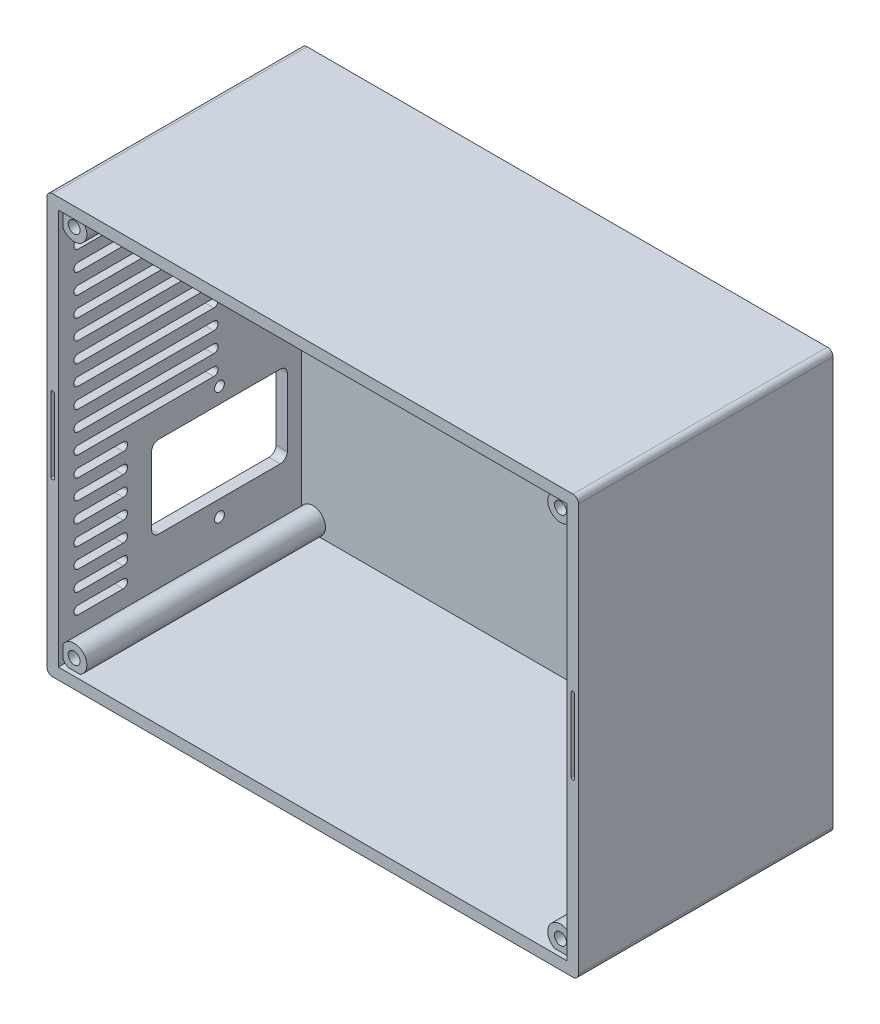
SolidWorks part; units mm, degrees
ref_plane "Alzado" through (0, 0, 0) normal (0, 0, 1) x (1, 0, 0)
ref_plane "Planta" through (0, 0, 0) normal (0, 1, 0) x (1, 0, 0)
ref_plane "Vista lateral" through (0, 0, 0) normal (1, 0, 0) x (0, 0, -1)
sketch "Croquis1" plane through (0, 0, 0) normal (0, 0, 1) x (1, 0, 0)
  line L0 (0, 0) -> (0, 140) construction
  line L5 (0, 140) -> (180, 140) construction
  line L6 (180, 140) -> (180, 0) construction
  line L7 (180, 0) -> (0, 0) construction
  line L9 (-4, 144) -> (184, 144)
  line L10 (-4, 144) -> (-4, -4)
  line L11 (-4, -4) -> (184, -4)
  line L12 (184, 144) -> (184, -4)
  dimension "D1" = 140
  dimension "D2" = 180
  dimension "D3" = 4
  dimension "D4" = 4
  dimension "D5" = 4
  dimension "D6" = 4
extrude "Saliente-Extruir1" add sketch "Croquis1" along normal blind 90 contours L9 L12 L11 L10
ref_plane "Plano2" through (0, 0, 4) normal (0, 0, -1) x (-1, 0, 0)
sketch "Croquis6" plane through (0, 0, 4) normal (0, 0, -1) x (-1, 0, 0)
  line L1 (0, 140) -> (-180, 140)
  line L2 (0, 140) -> (0, 0)
  line L3 (0, 0) -> (-180, 0)
  line L4 (-180, 140) -> (-180, 0)
  line L5 (4, 144) -> (-184, 144) construction
  line L6 (4, 144) -> (4, -4) construction
  line L7 (4, -4) -> (-184, -4) construction
  line L8 (-184, 144) -> (-184, -4) construction
  dimension "D3" = 4
  dimension "D1" = 4
  dimension "D2" = 4
  dimension "D4" = 4
extrude "Cortar-Extruir1" cut sketch "Croquis6" against normal through all
sketch "Croquis7" plane through (0, 0, 4) normal (0, 0, -1) x (-1, 0, 0)
  line L0 (0, 140) -> (-180, 140) construction
  line L1 (-4, 136) -> (-176, 136)
  line L2 (-4, 136) -> (-4, 4)
  line L3 (-4, 4) -> (-176, 4)
  line L4 (-176, 136) -> (-176, 4)
  line L5 (0, 0) -> (0, 140) construction
  line L6 (-180, 0) -> (0, 0) construction
  line L7 (-180, 140) -> (-180, 0) construction
  circle A0 centre (-4, 136) radius 4.4996
  circle A5 centre (-176, 136) radius 4.4996
  circle A6 centre (-176, 4) radius 4.4996
  circle A8 centre (-4, 4) radius 4.4996
  dimension "D3" = 4
  dimension "D1" = 4
  dimension "D4" = 4
  dimension "D7" = 8.9993
  dimension "D5" = 8.9993
  dimension "D6" = 8.9993
  dimension "D8" = 8.9993
  dimension "D2" = 4
extrude "Saliente-Extruir2" add sketch "Croquis7" against normal blind 84.4
sketch "Croquis9" plane through (0, 0, 4) normal (0, 0, -1) x (-1, 0, 0)
  line L1 (-4, 136) -> (-176, 136)
  line L2 (-4, 136) -> (-4, 4)
  line L3 (-4, 4) -> (-176, 4)
  line L4 (-176, 136) -> (-176, 4)
  circle A0 centre (-4, 136) radius 2.1
  circle A1 centre (-176, 136) radius 2.1
  circle A2 centre (-176, 4) radius 2.1
  circle A3 centre (-4, 4) radius 2.1
  dimension "D1" = 4.2
  dimension "D4" = 4.2
  dimension "D5" = 4.2
  dimension "D6" = 4.2
  dimension "D2" = 132
  dimension "D3" = 172
extrude "Cortar-Extruir3" cut sketch "Croquis9" against normal up to next contours A0 | A1 | A2 | A3
fillet "Redondeo1" radius 2 4 edges at (184, 144, 45) (184, -4, 45) (-4, -4, 45) (-4, 144, 45)
sketch "Croquis10" plane through (0, 0, 4) normal (0, 0, -1) x (-1, 0, 0)
  line L0 (2, 144) -> (-182, 144) construction
  line L1 (-16, 124) -> (-164, 124)
  line L2 (-16, 124) -> (-16, 16)
  line L3 (-16, 16) -> (-164, 16)
  line L4 (-164, 124) -> (-164, 16)
  line L5 (4, 142) -> (4, -2) construction
  line L6 (2, -4) -> (-182, -4) construction
  line L7 (-184, 142) -> (-184, -2) construction
  circle A0 centre (-16, 124) radius 7.5
  circle A1 centre (-164, 124) radius 7.5
  circle A2 centre (-164, 16) radius 7.5
  circle A3 centre (-16, 16) radius 7.5
  dimension "D5" = 15
  dimension "D6" = 15
  dimension "D7" = 15
  dimension "D8" = 15
  dimension "D1" = 20
  dimension "D2" = 20
  dimension "D3" = 20
  dimension "D4" = 20
extrude "Cortar-Extruir4" cut sketch "Croquis10" along normal through all from offset 2 contours A0 | A1 | A2 | A3
ref_plane "Plano3" through (-4, 0, 0) normal (-1, 0, 0) x (0, 0, 1)
sketch "Croquis11" plane through (-4, 0, 0) normal (-1, 0, 0) x (0, 0, 1)
  line L0 (9, 37.5) -> (57, 37.5) construction
  line L1 (11.5, 52) -> (54.5, 52)
  line L2 (9, 49.5) -> (9, 25.5)
  line L3 (11.5, 23) -> (54.5, 23)
  line L4 (57, 49.5) -> (57, 25.5)
  line L5 (33, 52) -> (33, 23) construction
  line L6 (0, 142) -> (0, -2) construction
  line L7 (0, -2) -> (90, -2) construction
  arc A0 (9, 25.5) -> (11.5, 23) centre (11.5, 25.5) ccw
  arc A1 (54.5, 23) -> (57, 25.5) centre (54.5, 25.5) ccw
  arc A2 (54.5, 52) -> (57, 49.5) centre (54.5, 49.5) cw
  arc A3 (11.5, 52) -> (9, 49.5) centre (11.5, 49.5) ccw
  circle A4 centre (33, 57.5) radius 1.75
  circle A5 centre (33, 17.5) radius 1.75
  point P8 (57, 23)
  point P11 (57, 52)
  point P14 (9, 52)
  point P27 (33, 48.1213)
  point P28 (33, 6.626)
  point P29 (0, 0)
  point P30 (0, 0)
  point P31 (0, 0)
  point P32 (0, 0)
  point P33 (0, 0)
  point P34 (0, 0)
  point P35 (33, 16.1617)
  point P36 (33, 40.8738)
  dimension "D3" = 2.5
  dimension "D4" = 9
  dimension "D5" = 25
  dimension "D6" = 20
  dimension "D8" = 3.5
  dimension "D9" = 3.5
  dimension "D1" = 48
  dimension "D2" = 29
  dimension "D7" = 20
sketch "Croquis12" plane through (0, 0, 4) normal (0, 0, -1) x (-1, 0, 0)
  line L0 (0, 140) -> (-180, 140) construction
  line L1 (-180, 133.9392) -> (-180, 6.0608) construction
  circle A1 centre (-93, 125) radius 2.1
  circle A2 centre (-93, 54) radius 2.1
  point P2 (0, 0)
  point P3 (0, 0)
  point P8 (0, 0)
  dimension "D3" = 15
  dimension "D4" = 4.2
  dimension "D1" = 4.2
  dimension "D2" = 71
  dimension "D5" = 87
ref_plane "Plano4" through (0, 140, 0) normal (0, -1, 0) x (-1, 0, 0)
sketch "Croquis15" plane through (0, 0, 4) normal (0, 0, -1) x (-1, 0, 0)
  line L0 (2, 144) -> (-182, 144) construction
  line L1 (-164, 114) -> (-124, 114)
  line L2 (-164, 114) -> (-164, 74)
  line L3 (-164, 74) -> (-124, 74)
  line L4 (-124, 114) -> (-124, 74)
  line L5 (-184, 142) -> (-184, -2) construction
  line L7 (-160.5, 110.5) -> (-127.5, 110.5)
  line L8 (-160.5, 110.5) -> (-160.5, 77.5)
  line L9 (-160.5, 77.5) -> (-127.5, 77.5)
  line L10 (-127.5, 110.5) -> (-127.5, 77.5)
  circle A0 centre (-160.5, 110.5) radius 1.75
  circle A1 centre (-127.5, 110.5) radius 1.75
  circle A2 centre (-127.5, 77.5) radius 1.75
  circle A3 centre (-160.5, 77.5) radius 1.75
  dimension "D4" = 20
  dimension "D9" = 3.5
  dimension "D10" = 3.5
  dimension "D11" = 3.5
  dimension "D12" = 3.5
  dimension "D1" = 40
  dimension "D2" = 40
  dimension "D3" = 30
  dimension "D5" = 33
  dimension "D6" = 33
  dimension "D7" = 3.5
  dimension "D8" = 3.5
extrude "Cortar-Extruir19" cut sketch "Croquis15" along normal up to next (4 mm away) contours A0 | A1 | A3 | A2
sketch "Croquis17" plane through (0, 0, 4) normal (0, 0, -1) x (-1, 0, 0)
  line L0 (-164, 94) -> (-124, 94) construction
  line L1 (-164, 114) -> (-164, 74) construction
  line L2 (-124, 114) -> (-124, 74) construction
  line L3 (-144, 114) -> (-144, 74) construction
  line L4 (-164, 114) -> (-124, 114) construction
  line L5 (-164, 74) -> (-124, 74) construction
  line L6 (-144, 113.1) -> (-144, 103.1) construction
  line L11 (-143.25, 113.1) -> (-143.25, 103.1)
  line L12 (-144.75, 113.1) -> (-144.75, 103.1)
  line L13 (-140.1573, 112.7245) -> (-142.5504, 103.0151)
  line L14 (-138.7009, 112.3655) -> (-141.094, 102.6561)
  line L15 (-139.4291, 112.545) -> (-141.8222, 102.8356) construction
  line L16 (-135.7879, 111.2608) -> (-140.4351, 102.4062)
  line L17 (-134.4597, 110.5637) -> (-139.1069, 101.7091)
  line L18 (-135.1238, 110.9122) -> (-139.771, 102.0576) construction
  line L19 (-131.8957, 108.7939) -> (-138.527, 101.3088)
  line L20 (-130.773, 107.7992) -> (-137.4042, 100.3141)
  line L21 (-131.3344, 108.2966) -> (-137.9656, 100.8114) construction
  line L22 (-128.7071, 105.4673) -> (-136.9369, 99.7866)
  line L23 (-127.855, 104.2328) -> (-136.0848, 98.5522)
  line L24 (-128.281, 104.85) -> (-136.5108, 99.1694) construction
  line L25 (-126.4071, 101.4742) -> (-135.7573, 97.9282)
  line L26 (-125.8752, 100.0717) -> (-135.2254, 96.5256)
  line L27 (-126.1412, 100.773) -> (-135.4914, 97.2269) construction
  line L28 (-125.1297, 97.0468) -> (-135.0568, 95.8414)
  line L29 (-124.9489, 95.5577) -> (-134.8759, 94.3524)
  line L30 (-125.0393, 96.3023) -> (-134.9663, 95.0969) construction
  line L31 (-124.9489, 92.4423) -> (-134.8759, 93.6476)
  line L32 (-125.1297, 90.9532) -> (-135.0568, 92.1586)
  line L33 (-125.0393, 91.6977) -> (-134.9663, 92.9031) construction
  line L34 (-125.8752, 87.9283) -> (-135.2254, 91.4744)
  line L35 (-126.4071, 86.5258) -> (-135.7573, 90.0718)
  line L36 (-126.1412, 87.227) -> (-135.4914, 90.7731) construction
  line L37 (-127.855, 83.7672) -> (-136.0848, 89.4478)
  line L38 (-128.7071, 82.5327) -> (-136.9369, 88.2134)
  line L39 (-128.281, 83.15) -> (-136.5108, 88.8306) construction
  line L40 (-130.773, 80.2008) -> (-137.4042, 87.6859)
  line L41 (-131.8957, 79.2061) -> (-138.527, 86.6912)
  line L42 (-131.3344, 79.7034) -> (-137.9656, 87.1886) construction
  line L43 (-134.4597, 77.4363) -> (-139.1069, 86.2909)
  line L44 (-135.7879, 76.7392) -> (-140.4351, 85.5938)
  line L45 (-135.1238, 77.0878) -> (-139.771, 85.9424) construction
  line L46 (-138.7009, 75.6345) -> (-141.094, 85.3439)
  line L47 (-140.1573, 75.2755) -> (-142.5504, 84.9849)
  line L48 (-139.4291, 75.455) -> (-141.8222, 85.1644) construction
  line L49 (-143.25, 74.9) -> (-143.25, 84.9)
  line L50 (-144.75, 74.9) -> (-144.75, 84.9)
  line L51 (-144, 74.9) -> (-144, 84.9) construction
  line L52 (-147.8427, 75.2755) -> (-145.4496, 84.9849)
  line L53 (-149.2991, 75.6345) -> (-146.906, 85.3439)
  line L54 (-148.5709, 75.455) -> (-146.1778, 85.1644) construction
  line L55 (-152.2121, 76.7392) -> (-147.5649, 85.5938)
  line L56 (-153.5403, 77.4363) -> (-148.8931, 86.2909)
  line L57 (-152.8762, 77.0878) -> (-148.229, 85.9424) construction
  line L58 (-156.1043, 79.2061) -> (-149.473, 86.6912)
  line L59 (-157.227, 80.2008) -> (-150.5958, 87.6859)
  line L60 (-156.6656, 79.7034) -> (-150.0344, 87.1886) construction
  line L61 (-159.2929, 82.5327) -> (-151.0631, 88.2134)
  line L62 (-160.145, 83.7672) -> (-151.9152, 89.4478)
  line L63 (-159.719, 83.15) -> (-151.4892, 88.8306) construction
  line L64 (-161.5929, 86.5258) -> (-152.2427, 90.0718)
  line L65 (-162.1248, 87.9283) -> (-152.7746, 91.4744)
  line L66 (-161.8588, 87.227) -> (-152.5086, 90.7731) construction
  line L67 (-162.8703, 90.9532) -> (-152.9432, 92.1586)
  line L68 (-163.0511, 92.4423) -> (-153.1241, 93.6476)
  line L69 (-162.9607, 91.6977) -> (-153.0337, 92.9031) construction
  line L70 (-163.0511, 95.5577) -> (-153.1241, 94.3524)
  line L71 (-162.8703, 97.0468) -> (-152.9432, 95.8414)
  line L72 (-162.9607, 96.3023) -> (-153.0337, 95.0969) construction
  line L73 (-162.1248, 100.0717) -> (-152.7746, 96.5256)
  line L74 (-161.5929, 101.4742) -> (-152.2427, 97.9282)
  line L75 (-161.8588, 100.773) -> (-152.5086, 97.2269) construction
  line L76 (-160.145, 104.2328) -> (-151.9152, 98.5522)
  line L77 (-159.2929, 105.4673) -> (-151.0631, 99.7866)
  line L78 (-159.719, 104.85) -> (-151.4892, 99.1694) construction
  line L79 (-157.227, 107.7992) -> (-150.5958, 100.3141)
  line L80 (-156.1043, 108.7939) -> (-149.473, 101.3088)
  line L81 (-156.6656, 108.2966) -> (-150.0344, 100.8114) construction
  line L82 (-153.5403, 110.5637) -> (-148.8931, 101.7091)
  line L83 (-152.2121, 111.2608) -> (-147.5649, 102.4062)
  line L84 (-152.8762, 110.9122) -> (-148.229, 102.0576) construction
  line L85 (-149.2991, 112.3655) -> (-146.906, 102.6561)
  line L86 (-147.8427, 112.7245) -> (-145.4496, 103.0151)
  line L87 (-148.5709, 112.545) -> (-146.1778, 102.8356) construction
  arc A1 (-143.25, 113.1) -> (-144.75, 113.1) centre (-144, 113.1) ccw
  arc A2 (-144.75, 103.1) -> (-143.25, 103.1) centre (-144, 103.1) ccw
  arc A3 (-138.7009, 112.3655) -> (-140.1573, 112.7245) centre (-139.4291, 112.545) ccw
  arc A4 (-142.5504, 103.0151) -> (-141.094, 102.6561) centre (-141.8222, 102.8356) ccw
  arc A5 (-134.4597, 110.5637) -> (-135.7879, 111.2608) centre (-135.1238, 110.9122) ccw
  arc A6 (-140.4351, 102.4062) -> (-139.1069, 101.7091) centre (-139.771, 102.0576) ccw
  arc A7 (-130.773, 107.7992) -> (-131.8957, 108.7939) centre (-131.3344, 108.2966) ccw
  arc A8 (-138.527, 101.3088) -> (-137.4042, 100.3141) centre (-137.9656, 100.8114) ccw
  arc A9 (-127.855, 104.2328) -> (-128.7071, 105.4673) centre (-128.281, 104.85) ccw
  arc A10 (-136.9369, 99.7866) -> (-136.0848, 98.5522) centre (-136.5108, 99.1694) ccw
  arc A11 (-125.8752, 100.0717) -> (-126.4071, 101.4742) centre (-126.1412, 100.773) ccw
  arc A12 (-135.7573, 97.9282) -> (-135.2254, 96.5256) centre (-135.4914, 97.2269) ccw
  arc A13 (-124.9489, 95.5577) -> (-125.1297, 97.0468) centre (-125.0393, 96.3023) ccw
  arc A14 (-135.0568, 95.8414) -> (-134.8759, 94.3524) centre (-134.9663, 95.0969) ccw
  arc A15 (-125.1297, 90.9532) -> (-124.9489, 92.4423) centre (-125.0393, 91.6977) ccw
  arc A16 (-134.8759, 93.6476) -> (-135.0568, 92.1586) centre (-134.9663, 92.9031) ccw
  arc A17 (-126.4071, 86.5258) -> (-125.8752, 87.9283) centre (-126.1412, 87.227) ccw
  arc A18 (-135.2254, 91.4744) -> (-135.7573, 90.0718) centre (-135.4914, 90.7731) ccw
  arc A19 (-128.7071, 82.5327) -> (-127.855, 83.7672) centre (-128.281, 83.15) ccw
  arc A20 (-136.0848, 89.4478) -> (-136.9369, 88.2134) centre (-136.5108, 88.8306) ccw
  arc A21 (-131.8957, 79.2061) -> (-130.773, 80.2008) centre (-131.3344, 79.7034) ccw
  arc A22 (-137.4042, 87.6859) -> (-138.527, 86.6912) centre (-137.9656, 87.1886) ccw
  arc A23 (-135.7879, 76.7392) -> (-134.4597, 77.4363) centre (-135.1238, 77.0878) ccw
  arc A24 (-139.1069, 86.2909) -> (-140.4351, 85.5938) centre (-139.771, 85.9424) ccw
  arc A25 (-140.1573, 75.2755) -> (-138.7009, 75.6345) centre (-139.4291, 75.455) ccw
  arc A26 (-141.094, 85.3439) -> (-142.5504, 84.9849) centre (-141.8222, 85.1644) ccw
  arc A27 (-144.75, 74.9) -> (-143.25, 74.9) centre (-144, 74.9) ccw
  arc A28 (-143.25, 84.9) -> (-144.75, 84.9) centre (-144, 84.9) ccw
  arc A29 (-149.2991, 75.6345) -> (-147.8427, 75.2755) centre (-148.5709, 75.455) ccw
  arc A30 (-145.4496, 84.9849) -> (-146.906, 85.3439) centre (-146.1778, 85.1644) ccw
  arc A31 (-153.5403, 77.4363) -> (-152.2121, 76.7392) centre (-152.8762, 77.0878) ccw
  arc A32 (-147.5649, 85.5938) -> (-148.8931, 86.2909) centre (-148.229, 85.9424) ccw
  arc A33 (-157.227, 80.2008) -> (-156.1043, 79.2061) centre (-156.6656, 79.7034) ccw
  arc A34 (-149.473, 86.6912) -> (-150.5958, 87.6859) centre (-150.0344, 87.1886) ccw
  arc A35 (-160.145, 83.7672) -> (-159.2929, 82.5327) centre (-159.719, 83.15) ccw
  arc A36 (-151.0631, 88.2134) -> (-151.9152, 89.4478) centre (-151.4892, 88.8306) ccw
  arc A37 (-162.1248, 87.9283) -> (-161.5929, 86.5258) centre (-161.8588, 87.227) ccw
  arc A38 (-152.2427, 90.0718) -> (-152.7746, 91.4744) centre (-152.5086, 90.7731) ccw
  arc A39 (-163.0511, 92.4423) -> (-162.8703, 90.9532) centre (-162.9607, 91.6977) ccw
  arc A40 (-152.9432, 92.1586) -> (-153.1241, 93.6476) centre (-153.0337, 92.9031) ccw
  arc A41 (-162.8703, 97.0468) -> (-163.0511, 95.5577) centre (-162.9607, 96.3023) ccw
  arc A42 (-153.1241, 94.3524) -> (-152.9432, 95.8414) centre (-153.0337, 95.0969) ccw
  arc A43 (-161.5929, 101.4742) -> (-162.1248, 100.0717) centre (-161.8588, 100.773) ccw
  arc A44 (-152.7746, 96.5256) -> (-152.2427, 97.9282) centre (-152.5086, 97.2269) ccw
  arc A45 (-159.2929, 105.4673) -> (-160.145, 104.2328) centre (-159.719, 104.85) ccw
  arc A46 (-151.9152, 98.5522) -> (-151.0631, 99.7866) centre (-151.4892, 99.1694) ccw
  arc A47 (-156.1043, 108.7939) -> (-157.227, 107.7992) centre (-156.6656, 108.2966) ccw
  arc A48 (-150.5958, 100.3141) -> (-149.473, 101.3088) centre (-150.0344, 100.8114) ccw
  arc A49 (-152.2121, 111.2608) -> (-153.5403, 110.5637) centre (-152.8762, 110.9122) ccw
  arc A50 (-148.8931, 101.7091) -> (-147.5649, 102.4062) centre (-148.229, 102.0576) ccw
  arc A51 (-147.8427, 112.7245) -> (-149.2991, 112.3655) centre (-148.5709, 112.545) ccw
  arc A52 (-146.906, 102.6561) -> (-145.4496, 103.0151) centre (-146.1778, 102.8356) ccw
  point P12 (-144, 94)
  point P17 (-144, 108.1)
  point P26 (-140.6256, 107.6903)
  point P33 (-137.4474, 106.4849)
  point P40 (-134.65, 104.554)
  point P47 (-132.3959, 102.0097)
  point P54 (-130.8163, 98.9999)
  point P61 (-130.0028, 95.6996)
  point P68 (-130.0028, 92.3004)
  point P75 (-130.8163, 89.0001)
  point P82 (-132.3959, 85.9903)
  point P89 (-134.65, 83.446)
  point P96 (-137.4474, 81.5151)
  point P103 (-140.6256, 80.3097)
  point P110 (-144, 79.9)
  point P117 (-147.3744, 80.3097)
  point P124 (-150.5526, 81.5151)
  point P131 (-153.35, 83.446)
  point P138 (-155.6041, 85.9903)
  point P145 (-157.1837, 89.0001)
  point P152 (-157.9972, 92.3004)
  point P159 (-157.9972, 95.6996)
  point P166 (-157.1837, 98.9999)
  point P173 (-155.6041, 102.0097)
  point P180 (-153.35, 104.554)
  point P187 (-150.5526, 106.4849)
  point P194 (-147.3744, 107.6903)
  point P199 (-144, 94)
  dimension "D2" = 10
  dimension "D1" = 1.5
  dimension "D3" = 0.9
  dimension "D4" = 26
extrude "Cortar-Extruir23" cut sketch "Croquis17" along normal up to next (4 mm away)
pattern_linear "MatrizL1" count 2 spacing 47.5 along (0, -1, 0) of "Cortar-Extruir23", "Cortar-Extruir19"
ref_plane "Plano5" through (0, 0, 90) normal (0, 0, 1) x (1, 0, 0)
sketch "Croquis18" plane through (0, 0, 90) normal (0, 0, 1) x (1, 0, 0)
  line L0 (-4, 70) -> (0, 70) construction
  line L1 (-4, 142) -> (-4, -2) construction
  line L2 (0, 6.0608) -> (0, 133.9392) construction
  line L3 (184, 70) -> (180, 70) construction
  line L4 (184, 142) -> (184, -2) construction
  line L5 (180, 140) -> (180, 0) construction
  line L6 (-2, 57) -> (-2, 83) construction
  line L7 (-2.6, 57) -> (-2.6, 83)
  line L8 (-1.4, 57) -> (-1.4, 83)
  line L9 (182, 57) -> (182, 83) construction
  line L10 (181.4, 57) -> (181.4, 83)
  line L11 (182.6, 57) -> (182.6, 83)
  arc A0 (-2.6, 57) -> (-1.4, 57) centre (-2, 57) ccw
  arc A1 (-1.4, 83) -> (-2.6, 83) centre (-2, 83) ccw
  arc A2 (181.4, 57) -> (182.6, 57) centre (182, 57) ccw
  arc A3 (182.6, 83) -> (181.4, 83) centre (182, 83) ccw
  point P14 (-2, 70)
  point P20 (182, 70)
  dimension "D1" = 26
  dimension "D2" = 1.2
  dimension "D3" = 26
  dimension "D4" = 1.2
extrude "Cortar-Extruir24" cut sketch "Croquis18" against normal blind 1.8
extrude "Cortar-Extruir25" cut sketch "Croquis11" against normal up to next
sketch "Croquis19" plane through (-4, 0, 0) normal (-1, 0, 0) x (0, 0, 1)
  line L0 (35, 126) -> (83, 126) construction
  line L3 (67, 19.5) -> (83, 19.5)
  line L4 (35, 119) -> (83, 119) construction
  line L5 (0, 144) -> (90, 144) construction
  line L6 (35, 127.5) -> (83, 127.5)
  line L7 (0, 142) -> (0, -2) construction
  line L8 (35, 124.5) -> (83, 124.5)
  line L11 (90, 142) -> (0, 142) construction
  line L14 (35, 120.5) -> (83, 120.5)
  line L17 (35, 117.5) -> (83, 117.5)
  line L20 (35, 112) -> (83, 112) construction
  line L23 (35, 113.5) -> (83, 113.5)
  line L26 (35, 110.5) -> (83, 110.5)
  line L29 (35, 105) -> (83, 105) construction
  line L32 (35, 106.5) -> (83, 106.5)
  line L35 (35, 103.5) -> (83, 103.5)
  line L38 (67, 22.5) -> (83, 22.5)
  line L43 (57, 37.5) -> (90, 37.5) construction
  line L44 (67, 21) -> (83, 21) construction
  line L45 (67, 26.5) -> (83, 26.5)
  line L46 (57, 25.5) -> (57, 49.5) construction
  line L47 (90, 142) -> (90, -2) construction
  line L48 (67, 14) -> (83, 14) construction
  line L51 (67, 15.5) -> (83, 15.5)
  line L52 (67, 12.5) -> (83, 12.5)
  line L53 (75, -2) -> (75, 144) construction
  line L54 (0, -2) -> (90, -2) construction
  line L55 (67, 29.5) -> (83, 29.5)
  line L56 (67, 28) -> (83, 28) construction
  line L57 (67, 33.5) -> (83, 33.5)
  line L58 (67, 36.5) -> (83, 36.5)
  line L59 (67, 35) -> (83, 35) construction
  line L60 (67, 40.5) -> (83, 40.5)
  line L61 (67, 43.5) -> (83, 43.5)
  line L62 (67, 42) -> (83, 42) construction
  line L63 (67, 47.5) -> (83, 47.5)
  line L64 (67, 50.5) -> (83, 50.5)
  line L65 (67, 49) -> (83, 49) construction
  line L66 (67, 54.5) -> (83, 54.5)
  line L67 (67, 57.5) -> (83, 57.5)
  line L68 (67, 56) -> (83, 56) construction
  line L70 (35, 98) -> (83, 98) construction
  line L71 (35, 99.5) -> (83, 99.5)
  line L72 (35, 96.5) -> (83, 96.5)
  line L73 (35, 91) -> (83, 91) construction
  line L74 (35, 92.5) -> (83, 92.5)
  line L75 (35, 89.5) -> (83, 89.5)
  line L76 (35, 84) -> (83, 84) construction
  line L77 (35, 85.5) -> (83, 85.5)
  line L78 (35, 82.5) -> (83, 82.5)
  line L79 (35, 77) -> (83, 77) construction
  line L80 (35, 78.5) -> (83, 78.5)
  line L81 (35, 75.5) -> (83, 75.5)
  line L82 (35, 70) -> (83, 70) construction
  line L83 (35, 71.5) -> (83, 71.5)
  line L84 (35, 68.5) -> (83, 68.5)
  line L85 (35, 63) -> (83, 63) construction
  line L86 (35, 64.5) -> (83, 64.5)
  line L87 (35, 61.5) -> (83, 61.5)
  arc A28 (67, 15.5) -> (67, 12.5) centre (67, 14) ccw
  arc A29 (83, 12.5) -> (83, 15.5) centre (83, 14) ccw
  arc A30 (67, 22.5) -> (67, 19.5) centre (67, 21) ccw
  arc A31 (83, 19.5) -> (83, 22.5) centre (83, 21) ccw
  arc A32 (67, 29.5) -> (67, 26.5) centre (67, 28) ccw
  arc A33 (83, 26.5) -> (83, 29.5) centre (83, 28) ccw
  arc A34 (67, 36.5) -> (67, 33.5) centre (67, 35) ccw
  arc A35 (83, 33.5) -> (83, 36.5) centre (83, 35) ccw
  arc A36 (67, 43.5) -> (67, 40.5) centre (67, 42) ccw
  arc A37 (83, 40.5) -> (83, 43.5) centre (83, 42) ccw
  arc A38 (67, 50.5) -> (67, 47.5) centre (67, 49) ccw
  arc A39 (83, 47.5) -> (83, 50.5) centre (83, 49) ccw
  arc A40 (67, 57.5) -> (67, 54.5) centre (67, 56) ccw
  arc A41 (83, 54.5) -> (83, 57.5) centre (83, 56) ccw
  arc A42 (35, 127.5) -> (35, 124.5) centre (35, 126) ccw
  arc A43 (83, 124.5) -> (83, 127.5) centre (83, 126) ccw
  arc A44 (35, 120.5) -> (35, 117.5) centre (35, 119) ccw
  arc A45 (83, 117.5) -> (83, 120.5) centre (83, 119) ccw
  arc A46 (35, 113.5) -> (35, 110.5) centre (35, 112) ccw
  arc A47 (83, 110.5) -> (83, 113.5) centre (83, 112) ccw
  arc A48 (35, 106.5) -> (35, 103.5) centre (35, 105) ccw
  arc A49 (83, 103.5) -> (83, 106.5) centre (83, 105) ccw
  arc A50 (35, 99.5) -> (35, 96.5) centre (35, 98) ccw
  arc A51 (83, 96.5) -> (83, 99.5) centre (83, 98) ccw
  arc A52 (35, 92.5) -> (35, 89.5) centre (35, 91) ccw
  arc A53 (83, 89.5) -> (83, 92.5) centre (83, 91) ccw
  arc A54 (35, 85.5) -> (35, 82.5) centre (35, 84) ccw
  arc A55 (83, 82.5) -> (83, 85.5) centre (83, 84) ccw
  arc A56 (35, 78.5) -> (35, 75.5) centre (35, 77) ccw
  arc A57 (83, 75.5) -> (83, 78.5) centre (83, 77) ccw
  arc A58 (35, 71.5) -> (35, 68.5) centre (35, 70) ccw
  arc A59 (83, 68.5) -> (83, 71.5) centre (83, 70) ccw
  arc A60 (35, 64.5) -> (35, 61.5) centre (35, 63) ccw
  arc A61 (83, 61.5) -> (83, 64.5) centre (83, 63) ccw
  point P2 (59, 126)
  point P9 (0, 0)
  point P17 (59, 119)
  point P19 (44.5, 114.5)
  point P25 (59, 112)
  point P26 (44.5, 107.5)
  point P33 (44.5, 100.5)
  point P34 (59, 105)
  point P40 (44.5, 93.5)
  point P42 (59, 98)
  point P49 (59, 91)
  point P56 (59, 84)
  point P63 (59, 77)
  point P70 (59, 70)
  point P77 (59, 63)
  point P82 (44.5, 121.5)
  point P93 (75, 14)
  point P106 (75, 21)
  point P113 (75, 28)
  point P120 (75, 35)
  point P127 (75, 42)
  point P134 (75, 49)
  point P141 (75, 56)
  point P146 (40, 58.5)
  point P153 (40, 58.5)
  point P160 (40, 58.5)
  point P167 (40, 58.5)
  point P174 (44.5, 58.5)
  point P181 (44.5, 58.5)
  point P188 (44.5, 58.5)
  point P195 (44.5, 58.5)
  point P202 (44.5, 58.5)
  point P209 (44.5, 114.5)
  point P216 (44.5, 107.5)
  point P223 (44.5, 100.5)
  point P230 (44.5, 93.5)
  point P237 (44.5, 121.5)
  point P244 (44.5, 58.5)
  dimension "D2" = 3
  dimension "D4" = 10
  dimension "D9" = 7
  dimension "D1" = 4
  dimension "D3" = 14.5
  dimension "D5" = 18
  dimension "D6" = 16
  dimension "D7" = 35
  dimension "D8" = 3
extrude "Cortar-Extruir26" cut sketch "Croquis19" against normal up to next
extrude "Cortar-Extruir27" cut sketch "Croquis12" along normal up to next
ref_plane "Plano8" through (0, -4, 0) normal (0, -1, 0) x (-1, 0, 0)
sketch "Croquis21" plane through (0, -4, 0) normal (0, -1, 0) x (-1, 0, 0)
  line L0 (-182, 0) -> (-182, -90) construction
  line L1 (-142, -15) -> (-38, -15)
  line L2 (-142, -15) -> (-142, -75)
  line L3 (-142, -75) -> (-38, -75)
  line L4 (-38, -15) -> (-38, -75)
  line L5 (2, -90) -> (2, 0) construction
  line L6 (2, -90) -> (-182, -90) construction
  line L7 (2, 0) -> (-182, 0) construction
  dimension "D1" = 40
  dimension "D2" = 40
  dimension "D3" = 15
  dimension "D4" = 15
extrude "Cortar-Extruir28" cut sketch "Croquis21" against normal blind 0.75
equation "\"D4@Croquis1\"=\"D3@Croquis1\""
equation "\"D5@Croquis1\"=\"D3@Croquis1\""
equation "\"D6@Croquis1\"=\"D3@Croquis1\""
equation "\"D2@Croquis6\"=\"D1@Croquis6\""
equation "\"D3@Croquis6\"=\"D1@Croquis6\""
equation "\"D4@Croquis6\"=\"D1@Croquis6\""
equation "\"D2@Croquis7\"=\"D1@Croquis7\""
equation "\"D3@Croquis7\"=\"D1@Croquis7\""
equation "\"D4@Croquis7\"=\"D1@Croquis7\""
equation "\"D2@Croquis10\"=\"D1@Croquis10\""
equation "\"D3@Croquis10\"=\"D1@Croquis10\""
equation "\"D4@Croquis10\"=\"D1@Croquis10\""
equation "\"D5@Croquis7\"=\"D7@Croquis7\""
equation "\"D6@Croquis7\"=\"D7@Croquis7\""
equation "\"D8@Croquis7\"=\"D7@Croquis7\""
equation "\"D4@Croquis9\"=\"D1@Croquis9\""
equation "\"D5@Croquis9\"=\"D1@Croquis9\""
equation "\"D6@Croquis9\"=\"D1@Croquis9\""
equation "\"D6@Croquis10\"=\"D5@Croquis10\""
equation "\"D7@Croquis10\"=\"D5@Croquis10\""
equation "\"D8@Croquis10\"=\"D5@Croquis10\""
equation "\"D10@Croquis15\"=\"D9@Croquis15\""
equation "\"D11@Croquis15\"=\"D9@Croquis15\""
equation "\"D12@Croquis15\"=\"D9@Croquis15\""
